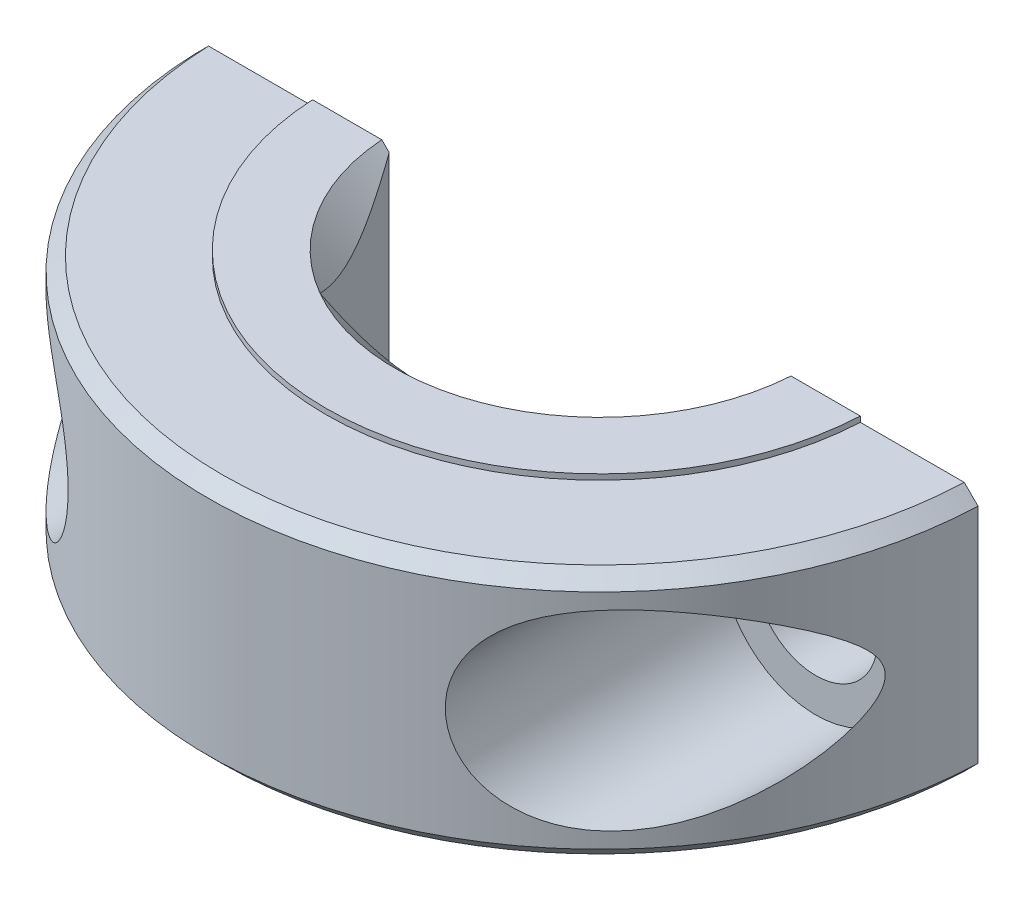
SolidWorks part; units mm, degrees
ref_plane "Front Plane" through (0, 0, 0) normal (0, 0, 1) x (1, 0, 0)
ref_plane "Top Plane" through (0, 0, 0) normal (0, 1, 0) x (1, 0, 0)
ref_plane "Right Plane" through (0, 0, 0) normal (1, 0, 0) x (0, 0, -1)
ref_plane "Plane9" through (0, 4.7625, 0) normal (0, 1, 0) x (1, 0, 0)
sketch "Sketch32" plane through (0, 4.7625, 0) normal (0, 1, 0) x (1, 0, 0)
  line L0 (14.2787, -0.5) -> (7.1903, -0.5)
  line L1 (7.1903, -0.5) -> (3.7395, -6.477)
  line L2 (3.7395, -6.477) -> (-3.7395, -6.477)
  line L3 (-3.7395, -6.477) -> (-7.1903, -0.5)
  line L4 (-7.1903, -0.5) -> (-14.2787, -0.5)
  arc A0 (-14.2787, -0.5) -> (14.2787, -0.5) centre (0, 0) ccw
  point P7 (0, 0)
  point P8 (0, 0)
  dimension "D1" = 14.2875
  dimension "D2" = 7.0884
  dimension "D3" = 10.5393
  dimension "D4" = 14.2787
  dimension "D5" = 18.0182
  dimension "D6" = 21.4691
  dimension "D7" = 5.977
extrude "Boss-Extrude1" add sketch "Sketch32" against normal blind 9.525
ref_plane "Plane10" through (0, 0, 0) normal (0.0669, 0, -0.9978) x (-0.9978, 0, -0.0669)
sketch "Sketch37" plane through (0, 0, 0) normal (0.0669, 0, -0.9978) x (-0.9978, 0, -0.0669)
  line L0 (0, -4.7625) -> (0, -3.7625)
  line L1 (0, -3.7625) -> (-6.477, -3.7625)
  line L2 (-6.477, -3.7625) -> (-7.477, -4.7625)
  line L3 (-7.477, -4.7625) -> (0, -4.7625)
  line L4 (0, -4.7625) -> (0, -3.7625) construction
  dimension "D1" = 6.477
  dimension "D2" = 7.477
  dimension "D3" = 1
revolve "Cut-Revolve4" cut sketch "Sketch37" angle 360 about L4
ref_plane "Plane11" through (0, 0, 0) normal (-0.0669, 0, -0.9978) x (-0.9978, 0, 0.0669)
sketch "Sketch43" plane through (0, 0, 0) normal (-0.0669, 0, -0.9978) x (-0.9978, 0, 0.0669)
  line L0 (0, 4.7625) -> (0, 3.7625)
  line L1 (0, 3.7625) -> (6.477, 3.7625)
  line L2 (6.477, 3.7625) -> (7.477, 4.7625)
  line L3 (7.477, 4.7625) -> (0, 4.7625)
  line L4 (0, 4.7625) -> (0, 3.7625) construction
  dimension "D1" = 6.477
  dimension "D2" = 7.477
  dimension "D3" = 1
revolve "Cut-Revolve5" cut sketch "Sketch43" angle 360 about L0
sketch "Sketch48" plane through (0, 4.7625, 0) normal (0, 1, 0) x (1, 0, 0)
  line L0 (14.2787, -0.5) -> (9.9875, -0.5)
  line L1 (-9.9875, -0.5) -> (-14.2787, -0.5)
  arc A0 (9.9875, -0.5) -> (-9.9875, -0.5) centre (0, 0) cw
  arc A1 (-14.2787, -0.5) -> (14.2787, -0.5) centre (0, 0) ccw
  dimension "D1" = 10
  dimension "D2" = 14.2875
  dimension "D3" = 4.2913
extrude "Cut-Extrude7" cut sketch "Sketch48" against normal blind 0.2
sketch "Sketch49" plane through (0, -4.7625, 0) normal (0, -1, 0) x (1, 0, 0)
  line L0 (9.9875, 0.5) -> (14.2787, 0.5)
  line L1 (-14.2787, 0.5) -> (-9.9875, 0.5)
  line L2 (14.2787, 0.5) -> (7.4603, 0.5) construction
  arc A0 (-9.9875, 0.5) -> (9.9875, 0.5) centre (0, 0) cw
  arc A1 (14.2787, 0.5) -> (-14.2787, 0.5) centre (0, 0) ccw
  dimension "D1" = 10
  dimension "D2" = 14.2875
  dimension "D3" = 4.2913
  dimension "D4" = 0.5
extrude "Cut-Extrude8" cut sketch "Sketch49" against normal blind 0.2
ref_plane "Plane12" through (0, 0, 12.5243) normal (0, 0, 1) x (1, 0, 0)
hole_wizard "CBORE for #8 Binding Head Machine Screw4" positions "Sketch51" profile "Sketch50" counterbore size "#8" standard "ANSI Inch"
sketch "Sketch51" plane through (0, 0, 12.5243) normal (0, 0, 1) x (1, 0, 0)
  point P0 (-10.3682, 0)
  point P1 (10.3682, 0)
sketch "Sketch50" plane through (-10.3682, 0, 12.5243) normal (1, 0, 0) x (0, -1, 0)
  line L0 (0, 0) -> (0, 12.0243)
  line L1 (0, 12.0243) -> (2.2479, 12.0243)
  line L3 (2.2479, 12.0243) -> (2.2479, 10.0243)
  line L4 (2.2479, 10.0243) -> (3.4925, 10.0243)
  line L5 (3.4925, 10.0243) -> (3.4925, 0)
  line L7 (3.4925, 0) -> (0, 0)
  line L11 (0, -6.35) -> (0, 107.95) construction
  dimension "Thru Hole Dia." = 4.4958
  dimension "Thru Hole Depth" = 12.0243
  dimension "C'Bore Dia." = 6.985
  dimension "C'Bore Depth" = 10.0243
chamfer "Chamfer4" distance 0.5 angle 45 2 edges at (0, 4.5625, 14.2875) (0, -4.5625, 14.2875)
